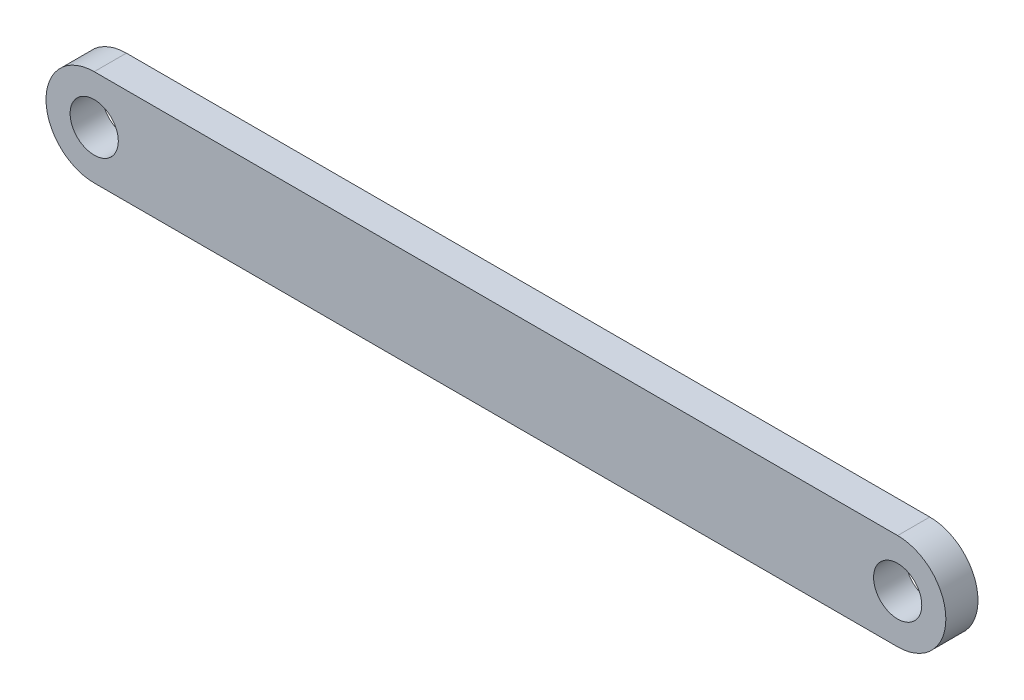
SolidWorks part; units mm, degrees
ref_plane "Front Plane" through (0, 0, 0) normal (0, 0, 1) x (1, 0, 0)
ref_plane "Top Plane" through (0, 0, 0) normal (0, 1, 0) x (1, 0, 0)
ref_plane "Right Plane" through (0, 0, 0) normal (1, 0, 0) x (0, 0, -1)
sketch "Sketch1" plane through (0, 0, 0) normal (0, 0, 1) x (1, 0, 0)
  line L0 (-25, 0) -> (25, 0) construction
  line L1 (-25, 3) -> (25, 3)
  line L2 (-25, -3) -> (25, -3)
  arc A0 (-25, 3) -> (-25, -3) centre (-25, 0) ccw
  arc A1 (25, -3) -> (25, 3) centre (25, 0) ccw
  circle A2 centre (-25, 0) radius 1.5
  circle A3 centre (25, 0) radius 1.5
  point P2 (0, 0)
  dimension "D1" = 3
  dimension "D2" = 3
  dimension "D3" = 50
extrude "Boss-Extrude1" add sketch "Sketch1" along normal blind 2
